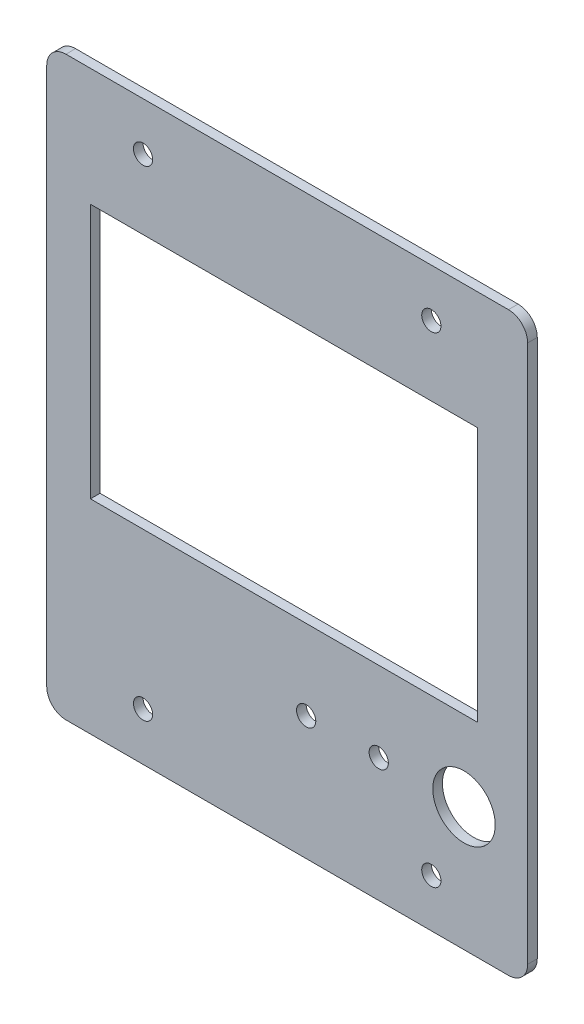
SolidWorks part; units mm, degrees
ref_plane "Front Plane" through (0, 0, 0) normal (0, 0, 1) x (1, 0, 0)
ref_plane "Top Plane" through (0, 0, 0) normal (0, 1, 0) x (1, 0, 0)
ref_plane "Right Plane" through (0, 0, 0) normal (1, 0, 0) x (0, 0, -1)
sketch "Sketch1" plane through (0, 0, 0) normal (0, 0, 1) x (1, 0, 0)
  line L0 (-30, 50) -> (30, -50) construction
  line L1 (-46.05, 60) -> (46.05, 60)
  line L2 (-50.05, 56) -> (-50.05, -56)
  line L3 (-46.05, -60) -> (46.05, -60)
  line L4 (50.05, 56) -> (50.05, -56)
  line L5 (50.05, 60) -> (-50.05, -60) construction
  line L6 (-39.95, 33.7) -> (-39.95, 30.5) construction
  line L7 (-40.95, 35.5) -> (39.65, 35.5)
  line L8 (-40.95, 35.5) -> (-40.95, -17.6)
  line L9 (-40.95, -17.6) -> (39.65, -17.6)
  line L10 (39.65, 35.5) -> (39.65, -17.6)
  line L11 (-39.95, 33.7) -> (-39.95, -15.8) construction
  line L12 (37.85, 34.5) -> (-39.15, 34.5) construction
  line L13 (-39.15, -16.6) -> (37.85, -16.6) construction
  line L14 (38.65, -15.8) -> (38.65, 33.7) construction
  circle A0 centre (-30, 50) radius 2
  circle A1 centre (-30, -50) radius 2
  circle A2 centre (30, -50) radius 2
  circle A3 centre (30, 50) radius 2
  arc A4 (46.05, 60) -> (50.05, 56) centre (46.05, 56) cw
  arc A5 (46.05, -60) -> (50.05, -56) centre (46.05, -56) ccw
  arc A6 (-50.05, -56) -> (-46.05, -60) centre (-46.05, -56) ccw
  arc A7 (-46.05, 60) -> (-50.05, 56) centre (-46.05, 56) ccw
  circle A8 centre (36.8, -34.25) radius 6.5
  circle A9 centre (19.05, -34.25) radius 2
  circle A10 centre (3.95, -34.25) radius 2
  point P23 (-50.05, 60)
  point P34 (-39.95, 32.1)
  dimension "D5" = 4
  dimension "D6" = 4
  dimension "D11" = 13
  dimension "D12" = 4
  dimension "D13" = 4
  dimension "D1" = 100.1
  dimension "D2" = 120
  dimension "D3" = 100
  dimension "D4" = 60
  dimension "D7" = 1
  dimension "D8" = 1
  dimension "D9" = 1
  dimension "D10" = 1
  dimension "D14" = 17.75
  dimension "D15" = 15.1
extrude "Boss-Extrude1" add sketch "Sketch1" along normal blind 2
